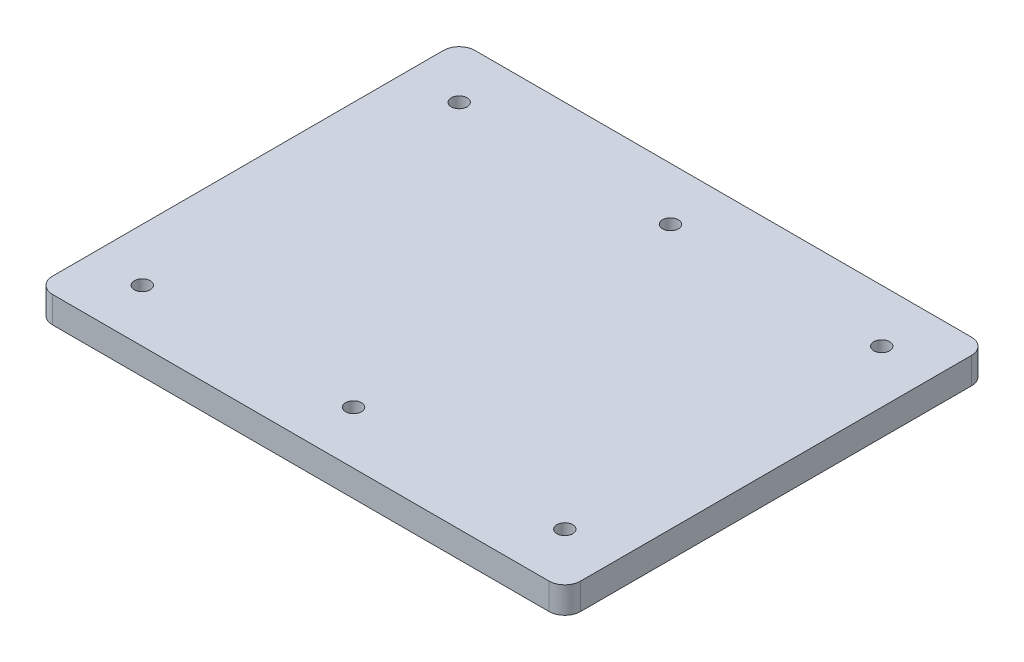
SolidWorks part; units mm, degrees
material "6061 合金"
ref_plane "前视基准面" through (0, 0, 0) normal (0, 0, 1) x (1, 0, 0)
ref_plane "上视基准面" through (0, 0, 0) normal (0, 1, 0) x (1, 0, 0)
ref_plane "右视基准面" through (0, 0, 0) normal (1, 0, 0) x (0, 0, -1)
sketch "草图2" plane through (0, 0, 0) normal (0, 1, 0) x (1, 0, 0)
  line L0 (0, 40) -> (100, 40) construction
  line L1 (0, 0) -> (100, 0)
  line L2 (0, 0) -> (0, 80)
  line L3 (0, 80) -> (100, 80)
  line L4 (100, 0) -> (100, 80)
  line L5 (50, 80) -> (50, 0) construction
  circle A0 centre (10, 10) radius 1.5
  circle A1 centre (50, 10) radius 1.5
  circle A2 centre (90, 10) radius 1.5
  circle A3 centre (90, 70) radius 1.5
  circle A4 centre (50, 70) radius 1.5
  circle A5 centre (10, 70) radius 1.5
  dimension "D3" = 10
  dimension "D1" = 100
  dimension "D2" = 80
  dimension "D4" = 10
  dimension "D5" = 3
extrude "凸台-拉伸1" add sketch "草图2" along normal blind 5
fillet "圆角1" radius 3 4 edges at (0, 2.5, -80) (100, 2.5, -80) (100, 2.5, 0) (0, 2.5, 0)
